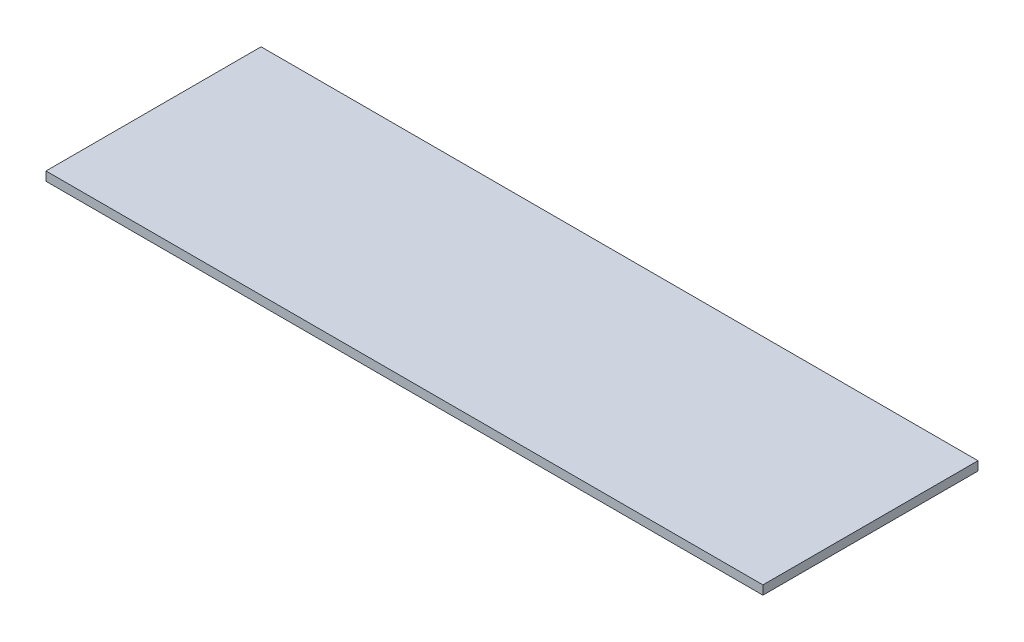
SolidWorks part; units mm, degrees
material "Custom Plastic"
ref_plane "Front Plane" through (0, 0, 0) normal (0, 0, 1) x (1, 0, 0)
ref_plane "Top Plane" through (0, 0, 0) normal (0, 1, 0) x (1, 0, 0)
ref_plane "Right Plane" through (0, 0, 0) normal (1, 0, 0) x (0, 0, -1)
sketch "Sketch1" plane through (0, 0, 0) normal (0, 1, 0) x (1, 0, 0)
  line L1 (508, 152.4) -> (0, 152.4)
  line L2 (508, 152.4) -> (508, 0)
  line L3 (508, 0) -> (0, 0)
  line L4 (0, 152.4) -> (0, 0)
extrude "Boss-Extrude1" add sketch "Sketch1" along normal blind 6.35
ref_plane "Plane1" through (0, 6.35, 0) normal (1, 0, 0) x (0, 0, -1)
sketch "Sketch3" plane through (0, 0, 0) normal (0, 1, 0) x (1, 0, 0)
  line L0 (254, 0) -> (254, -79.8219)
  line L1 (0, 0) -> (508, 0) construction
